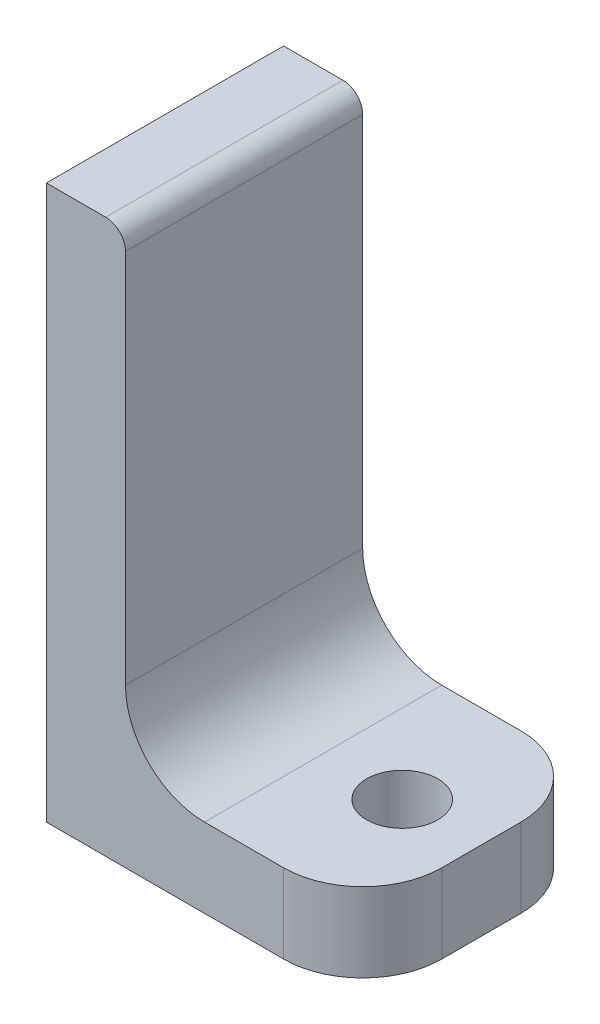
SolidWorks part; units mm, degrees
ref_plane "Front Plane" through (0, 0, 0) normal (0, 0, 1) x (1, 0, 0)
ref_plane "Top Plane" through (0, 0, 0) normal (0, 1, 0) x (1, 0, 0)
ref_plane "Right Plane" through (0, 0, 0) normal (1, 0, 0) x (0, 0, -1)
sketch "Sketch1" plane through (0, 0, 0) normal (0, 0, 1) x (1, 0, 0)
  line L0 (0, 35) -> (0, 0)
  line L1 (0, 0) -> (20, 0)
  line L3 (20, 5) -> (10, 5)
  line L4 (5, 10) -> (5, 33.75)
  line L5 (20, 5) -> (20, 0)
  line L6 (0, 35) -> (3.75, 35)
  arc A3 (10, 5) -> (5, 10) centre (10, 10) cw
  arc A8 (5, 33.75) -> (3.75, 35) centre (3.75, 33.75) ccw
  point P0 (7.5, 30.9879)
  dimension "D1" = 3.75
  dimension "D2" = 20
  dimension "D3" = 5
  dimension "D5" = 5
  dimension "D6" = 35
extrude "Boss-Extrude1" add sketch "Sketch1" along normal blind 15 contours L0 L1 L5 L3 A3 L4 A8 L6
sketch "Sketch2" plane through (0, 5, 0) normal (0, 1, 0) x (1, 0, 0)
  line L0 (10, -15) -> (10, 0) construction
  line L1 (20, 0) -> (10, 0) construction
  circle A0 centre (15, -7.5) radius 2.25
  point P4 (10, -7.5)
  point P7 (15, 0)
  dimension "D1" = 4.5
extrude "Cut-Extrude1" cut sketch "Sketch2" against normal up to next
fillet "Fillet1" radius 5 2 edges at (20, 2.5, 0) (20, 2.5, 15)
